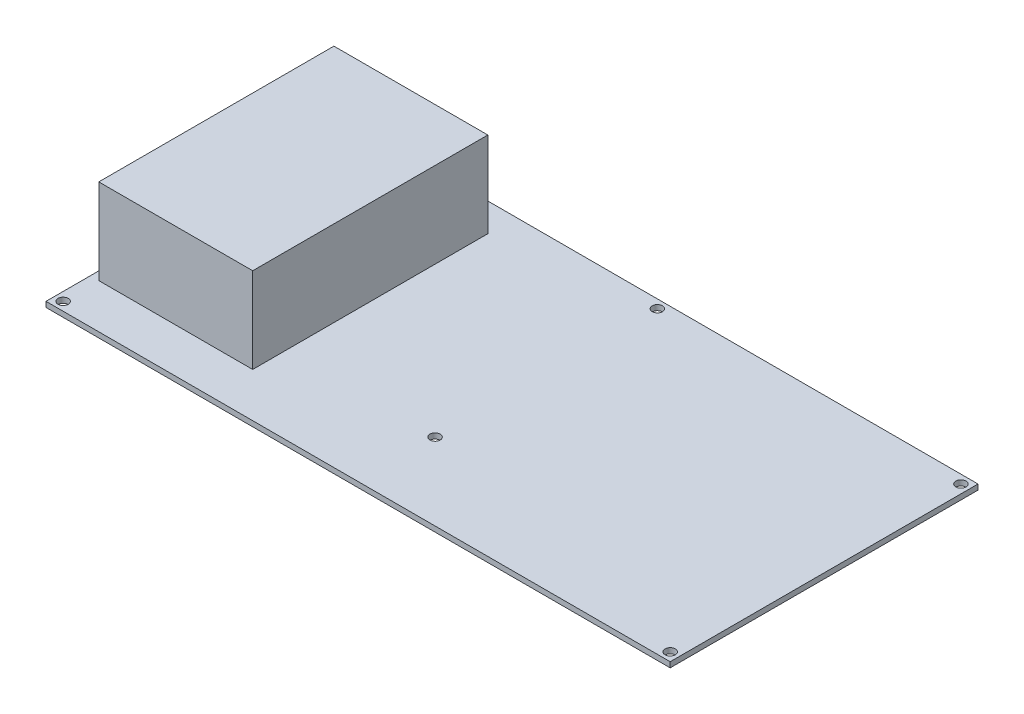
SolidWorks part; units mm, degrees
ref_plane "Front Plane" through (0, 0, 0) normal (0, 0, 1) x (1, 0, 0)
ref_plane "Top Plane" through (0, 0, 0) normal (0, 1, 0) x (1, 0, 0)
ref_plane "Right Plane" through (0, 0, 0) normal (1, 0, 0) x (0, 0, -1)
sketch "Sketch1" plane through (0, 0, 0) normal (0, 1, 0) x (1, 0, 0)
  line L0 (-93.5304, 45.9919) -> (86.8096, 45.9919) construction
  line L1 (-96.0704, 48.5319) -> (89.3496, 48.5319)
  line L2 (-96.0704, 48.5319) -> (-96.0704, -42.9081)
  line L3 (-96.0704, -42.9081) -> (89.3496, -42.9081)
  line L4 (89.3496, 48.5319) -> (89.3496, -42.9081)
  line L5 (86.8096, 45.9919) -> (86.8096, -40.3681) construction
  line L6 (-93.5304, -40.3681) -> (86.8096, -40.3681) construction
  line L7 (-93.5304, 45.9919) -> (-93.5304, -40.3681) construction
  circle A0 centre (-93.5304, 45.9919) radius 1.524
  circle A1 centre (86.8096, 45.9919) radius 1.524
  circle A2 centre (86.8096, -40.3681) radius 1.524
  circle A3 centre (-93.5304, -40.3681) radius 1.524
  circle A4 centre (-3.3604, 45.9919) radius 1.524
  circle A5 centre (-3.3604, -20.0481) radius 1.524
  dimension "D3" = 3.048
  dimension "D1" = 185.42
  dimension "D2" = 91.44
  dimension "D5" = 92.71
  dimension "D6" = 22.86
  dimension "D4" = 2.54
extrude "Boss-Extrude1" add sketch "Sketch1" along normal blind 1.5875
sketch "Sketch2" plane through (0, 1.5875, 0) normal (0, 1, 0) x (1, 0, 0)
  line L1 (-93.5628, 40.1139) -> (-47.8428, 40.1139)
  line L2 (-93.5628, 40.1139) -> (-93.5628, -29.7361)
  line L3 (-93.5628, -29.7361) -> (-47.8428, -29.7361)
  line L4 (-47.8428, 40.1139) -> (-47.8428, -29.7361)
  dimension "D1" = 45.72
  dimension "D2" = 69.85
extrude "Boss-Extrude2" add sketch "Sketch2" along normal blind 25.4
